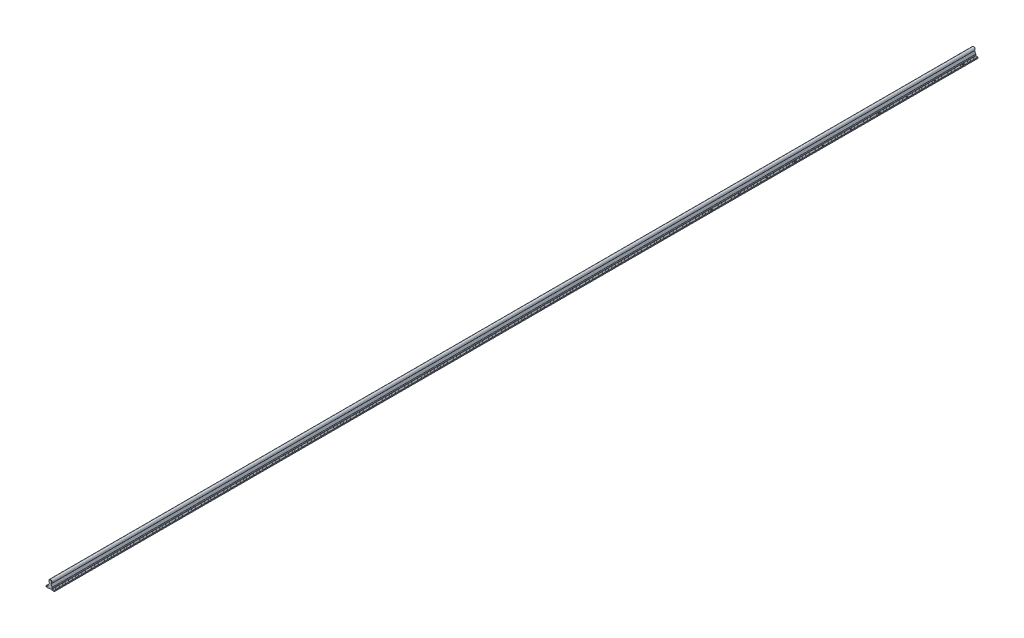
SolidWorks part; units mm, degrees
ref_plane "Plan de face" through (0, 0, 0) normal (0, 0, 1) x (1, 0, 0)
ref_plane "Plan de dessus" through (0, 0, 0) normal (0, 1, 0) x (1, 0, 0)
ref_plane "Plan de droite" through (0, 0, 0) normal (1, 0, 0) x (0, 0, -1)
sketch "Esquisse1" plane through (0, 0, 0) normal (0, 0, 1) x (1, 0, 0)
  line L0 (0, 0) -> (0, 3.5)
  line L1 (30, 0) -> (30, 4) construction
  line L2 (22.5, 4) -> (25.9, 4)
  line L3 (22, 4) -> (22, 9) construction
  line L4 (0, 0) -> (11, 0)
  line L5 (11, 0) -> (11, 0.5)
  line L6 (30, 0) -> (19, 0)
  line L7 (19, 0) -> (19, 0.5)
  line L8 (30, 0) -> (30, 3.5)
  line L9 (29.5, 4) -> (26.1, 4)
  line L10 (22, 4.5) -> (22, 8.8856)
  line L11 (11.5, 1) -> (18.5, 1)
  line L12 (0.5, 4) -> (3.9, 4)
  line L13 (8, 4.5) -> (8, 8.8856)
  line L14 (7.5, 4) -> (4.1, 4)
  line L15 (4.1, 4) -> (4.1, 3.8)
  line L16 (4.1, 3.8) -> (3.9, 3.8)
  line L17 (3.9, 3.8) -> (3.9, 4)
  line L18 (26.1, 4) -> (26.1, 3.8)
  line L19 (26.1, 3.8) -> (25.9, 3.8)
  line L20 (25.9, 3.8) -> (25.9, 4)
  line L23 (8.0497, 9.103) -> (12.3915, 18.0967)
  line L24 (21.9503, 9.103) -> (17.6085, 18.0967)
  arc A0 (0, 3.5) -> (0.5, 4) centre (0.5, 3.5) cw
  arc A1 (12.3915, 18.0967) -> (17.6085, 18.0967) centre (15, 23.5) cw
  arc A2 (29.5, 4) -> (30, 3.5) centre (29.5, 3.5) cw
  arc A3 (8, 4.5) -> (7.5, 4) centre (7.5, 4.5) cw
  arc A4 (22, 4.5) -> (22.5, 4) centre (22.5, 4.5) ccw
  arc A5 (18.5, 1) -> (19, 0.5) centre (18.5, 0.5) cw
  arc A6 (11.5, 1) -> (11, 0.5) centre (11.5, 0.5) ccw
  arc A7 (8.0497, 9.103) -> (8, 8.8856) centre (8.5, 8.8856) ccw
  arc A8 (22, 8.8856) -> (21.9503, 9.103) centre (21.5, 8.8856) ccw
  point P26 (0, 4)
  point P32 (8, 4)
  dimension "D1" = 0.5
  dimension "D2" = 0.5
  dimension "D3" = 0.5
  dimension "D4" = 0.5
  dimension "D5" = 0.5
  dimension "D6" = 0.5
  dimension "D7" = 0.5
  dimension "D8" = 0.5
extrude "Boss.-Extru.1" add sketch "Esquisse1" along normal blind 3300
chamfer "Chanfrein5" distance 1 angle 45 1 edges at (15, 29.5, 0)
chamfer "Chanfrein6" distance 1 angle 45 1 edges at (15, 29.5, 3300)
sketch "Esquisse2" plane through (0, 0, 0) normal (0, -1, 0) x (1, 0, 0)
  circle A2 centre (4, 850) radius 2.25
  circle A3 centre (26, 850) radius 2.25
  circle A4 centre (26, 950) radius 2.25
  circle A5 centre (4, 950) radius 2.25
extrude "Enlèv. mat.-Extru.1" cut sketch "Esquisse2" against normal up to next contours A2 | A3 | A4 | A5
pattern_linear "Répétition linéaire1" count 9 spacing 100 along (0, 0, -1) of "Enlèv. mat.-Extru.1"
